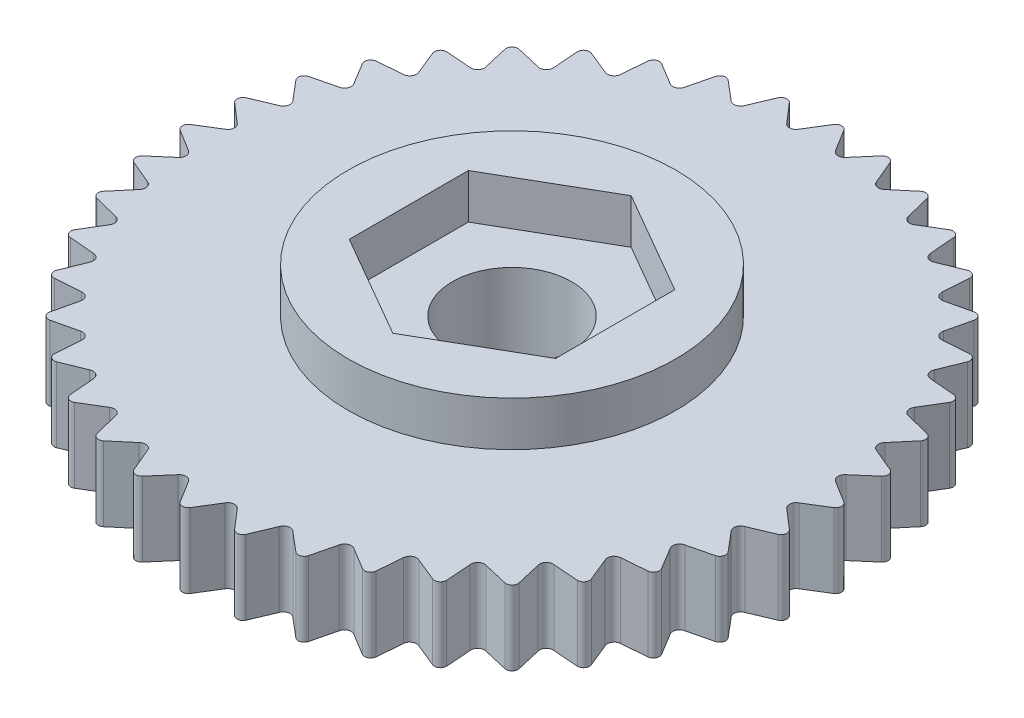
SolidWorks part; units mm, degrees
ref_plane "Front Plane" through (0, 0, 0) normal (0, 0, 1) x (1, 0, 0)
ref_plane "Top Plane" through (0, 0, 0) normal (0, 1, 0) x (1, 0, 0)
ref_plane "Right Plane" through (0, 0, 0) normal (1, 0, 0) x (0, 0, -1)
sketch "Sketch1" plane through (0, 0, 0) normal (0, 1, 0) x (1, 0, 0)
  line L0 (0, 11.25) -> (0, -11.25) construction
  line L1 (0, 11.25) -> (-1.7599, 11.1115) construction
  line L2 (-1.7599, 11.1115) -> (-3.4764, 10.6994) construction
  line L3 (-3.4764, 10.6994) -> (-5.1074, 10.0238) construction
  line L4 (-5.1074, 10.0238) -> (-6.6126, 9.1014) construction
  line L5 (-6.6126, 9.1014) -> (-7.955, 7.955) construction
  line L6 (-7.955, 7.955) -> (-9.1014, 6.6126) construction
  line L7 (-9.1014, 6.6126) -> (-10.0238, 5.1074) construction
  line L8 (-10.0238, 5.1074) -> (-10.6994, 3.4764) construction
  line L9 (-10.6994, 3.4764) -> (-11.1115, 1.7599) construction
  line L10 (-11.1115, 1.7599) -> (-11.25, 0) construction
  line L11 (-11.25, 0) -> (-11.1115, -1.7599) construction
  line L12 (-11.1115, -1.7599) -> (-10.6994, -3.4764) construction
  line L13 (-10.6994, -3.4764) -> (-10.0238, -5.1074) construction
  line L14 (-10.0238, -5.1074) -> (-9.1014, -6.6126) construction
  line L15 (-9.1014, -6.6126) -> (-7.955, -7.955) construction
  line L16 (-7.955, -7.955) -> (-6.6126, -9.1014) construction
  line L17 (-6.6126, -9.1014) -> (-5.1074, -10.0238) construction
  line L18 (-5.1074, -10.0238) -> (-3.4764, -10.6994) construction
  line L19 (-3.4764, -10.6994) -> (-1.7599, -11.1115) construction
  line L20 (-1.7599, -11.1115) -> (0, -11.25) construction
  line L21 (0, -11.25) -> (1.7599, -11.1115) construction
  line L22 (1.7599, -11.1115) -> (3.4764, -10.6994) construction
  line L23 (3.4764, -10.6994) -> (5.1074, -10.0238) construction
  line L24 (5.1074, -10.0238) -> (6.6126, -9.1014) construction
  line L25 (6.6126, -9.1014) -> (7.955, -7.955) construction
  line L26 (7.955, -7.955) -> (9.1014, -6.6126) construction
  line L27 (9.1014, -6.6126) -> (10.0238, -5.1074) construction
  line L28 (10.0238, -5.1074) -> (10.6994, -3.4764) construction
  line L29 (10.6994, -3.4764) -> (11.1115, -1.7599) construction
  line L30 (11.1115, -1.7599) -> (11.25, 0) construction
  line L31 (11.25, 0) -> (11.1115, 1.7599) construction
  line L32 (11.1115, 1.7599) -> (10.6994, 3.4764) construction
  line L33 (10.6994, 3.4764) -> (10.0238, 5.1074) construction
  line L34 (10.0238, 5.1074) -> (9.1014, 6.6126) construction
  line L35 (9.1014, 6.6126) -> (7.955, 7.955) construction
  line L36 (7.955, 7.955) -> (6.6126, 9.1014) construction
  line L37 (6.6126, 9.1014) -> (5.1074, 10.0238) construction
  line L38 (5.1074, 10.0238) -> (3.4764, 10.6994) construction
  line L39 (3.4764, 10.6994) -> (1.7599, 11.1115) construction
  line L40 (1.7599, 11.1115) -> (0, 11.25) construction
  line L41 (0, 11.25) -> (-0.7858, 9.984) construction
  line L42 (-0.8799, 11.1807) -> (-0.7858, 9.984) construction
  line L43 (0, 11.25) -> (0.7858, 9.984) construction
  line L44 (-0.7858, 9.984) -> (0.7858, 9.984) construction
  line L45 (-0.1688, 10.9781) -> (0.1688, 10.9781) construction
  line L46 (-0.806, 10.241) -> (-0.617, 10.2559) construction
  line L47 (-0.1688, 10.9781) -> (-0.6316, 10.2324)
  line L48 (0.8799, 11.1807) -> (0.7858, 9.984) construction
  line L49 (0.617, 10.2559) -> (0.806, 10.241) construction
  line L50 (0.1688, 10.9781) -> (0.617, 10.2559)
  line L51 (1.5507, 10.8694) -> (0.9769, 10.2052)
  line L52 (1.884, 10.8166) -> (2.2138, 10.0331)
  line L53 (3.2319, 10.493) -> (2.5613, 9.9267)
  line L54 (3.5529, 10.3887) -> (3.7561, 9.5633)
  line L55 (4.8336, 9.8582) -> (4.0826, 9.4039)
  line L56 (5.1343, 9.705) -> (5.2058, 8.858)
  line L57 (6.3162, 8.9807) -> (5.5035, 8.6494)
  line L58 (6.5893, 8.7823) -> (6.5274, 7.9345)
  line L59 (7.6434, 7.882) -> (6.7888, 7.682)
  line L60 (7.882, 7.6434) -> (7.6883, 6.8157)
  line L61 (8.7823, 6.5893) -> (7.9069, 6.5254)
  line L62 (8.9807, 6.3162) -> (8.6599, 5.5291)
  line L63 (9.705, 5.1343) -> (8.8304, 5.2082)
  line L64 (9.8582, 4.8336) -> (9.4182, 4.1063)
  line L65 (10.3887, 3.5529) -> (9.5364, 3.7627)
  line L66 (10.493, 3.2319) -> (9.9446, 2.5824)
  line L67 (10.8166, 1.884) -> (10.0076, 2.2245)
  line L68 (10.8694, 1.5507) -> (10.2262, 0.995)
  line L69 (10.9781, 0.1688) -> (10.2324, 0.6316)
  line L70 (10.9781, -0.1688) -> (10.2559, -0.617)
  line L71 (10.8694, -1.5507) -> (10.2052, -0.9769)
  line L72 (10.8166, -1.884) -> (10.0331, -2.2138)
  line L73 (10.493, -3.2319) -> (9.9267, -2.5613)
  line L74 (10.3887, -3.5529) -> (9.5633, -3.7561)
  line L75 (9.8582, -4.8336) -> (9.4039, -4.0826)
  line L76 (9.705, -5.1343) -> (8.858, -5.2058)
  line L77 (8.9807, -6.3162) -> (8.6494, -5.5035)
  line L78 (8.7823, -6.5893) -> (7.9345, -6.5274)
  line L79 (7.882, -7.6434) -> (7.682, -6.7888)
  line L80 (7.6434, -7.882) -> (6.8157, -7.6883)
  line L81 (6.5893, -8.7823) -> (6.5254, -7.9069)
  line L82 (6.3162, -8.9807) -> (5.5291, -8.6599)
  line L83 (5.1343, -9.705) -> (5.2082, -8.8304)
  line L84 (4.8336, -9.8582) -> (4.1063, -9.4182)
  line L85 (3.5529, -10.3887) -> (3.7627, -9.5364)
  line L86 (3.2319, -10.493) -> (2.5824, -9.9446)
  line L87 (1.884, -10.8166) -> (2.2245, -10.0076)
  line L88 (1.5507, -10.8694) -> (0.995, -10.2262)
  line L89 (0.1688, -10.9781) -> (0.6316, -10.2324)
  line L90 (-0.1688, -10.9781) -> (-0.617, -10.2559)
  line L91 (-1.5507, -10.8694) -> (-0.9769, -10.2052)
  line L92 (-1.884, -10.8166) -> (-2.2138, -10.0331)
  line L93 (-3.2319, -10.493) -> (-2.5613, -9.9267)
  line L94 (-3.5529, -10.3887) -> (-3.7561, -9.5633)
  line L95 (-4.8336, -9.8582) -> (-4.0826, -9.4039)
  line L96 (-5.1343, -9.705) -> (-5.2058, -8.858)
  line L97 (-6.3162, -8.9807) -> (-5.5035, -8.6494)
  line L98 (-6.5893, -8.7823) -> (-6.5274, -7.9345)
  line L99 (-7.6434, -7.882) -> (-6.7888, -7.682)
  line L100 (-7.882, -7.6434) -> (-7.6883, -6.8157)
  line L101 (-8.7823, -6.5893) -> (-7.9069, -6.5254)
  line L102 (-8.9807, -6.3162) -> (-8.6599, -5.5291)
  line L103 (-9.705, -5.1343) -> (-8.8304, -5.2082)
  line L104 (-9.8582, -4.8336) -> (-9.4182, -4.1063)
  line L105 (-10.3887, -3.5529) -> (-9.5364, -3.7627)
  line L106 (-10.493, -3.2319) -> (-9.9446, -2.5824)
  line L107 (-10.8166, -1.884) -> (-10.0076, -2.2245)
  line L108 (-10.8694, -1.5507) -> (-10.2262, -0.995)
  line L109 (-10.9781, -0.1688) -> (-10.2324, -0.6316)
  line L110 (-10.9781, 0.1688) -> (-10.2559, 0.617)
  line L111 (-10.8694, 1.5507) -> (-10.2052, 0.9769)
  line L112 (-10.8166, 1.884) -> (-10.0331, 2.2138)
  line L113 (-10.493, 3.2319) -> (-9.9267, 2.5613)
  line L114 (-10.3887, 3.5529) -> (-9.5633, 3.7561)
  line L115 (-9.8582, 4.8336) -> (-9.4039, 4.0826)
  line L116 (-9.705, 5.1343) -> (-8.858, 5.2058)
  line L117 (-8.9807, 6.3162) -> (-8.6494, 5.5035)
  line L118 (-8.7823, 6.5893) -> (-7.9345, 6.5274)
  line L119 (-7.882, 7.6434) -> (-7.682, 6.7888)
  line L120 (-7.6434, 7.882) -> (-6.8157, 7.6883)
  line L121 (-6.5893, 8.7823) -> (-6.5254, 7.9069)
  line L122 (-6.3162, 8.9807) -> (-5.5291, 8.6599)
  line L123 (-5.1343, 9.705) -> (-5.2082, 8.8304)
  line L124 (-4.8336, 9.8582) -> (-4.1063, 9.4182)
  line L125 (-3.5529, 10.3887) -> (-3.7627, 9.5364)
  line L126 (-3.2319, 10.493) -> (-2.5824, 9.9446)
  line L127 (-1.884, 10.8166) -> (-2.2245, 10.0076)
  line L128 (-1.5507, 10.8694) -> (-0.995, 10.2262)
  circle A0 centre (0, 0) radius 11.25 construction
  circle A1 centre (0, 0) radius 5.5
  arc A2 (-0.1688, 10.9781) -> (0.1688, 10.9781) centre (0, 10.87) cw
  arc A3 (-0.617, 10.2559) -> (-0.7979, 10.138) centre (-0.8156, 10.3629) cw
  arc A4 (0.617, 10.2559) -> (0.7979, 10.138) centre (0.8156, 10.3629) ccw
  arc A5 (0.995, 10.2262) -> (0.7979, 10.138) centre (0.8156, 10.3629) cw
  arc A6 (1.5507, 10.8694) -> (1.884, 10.8166) centre (1.7004, 10.7362) cw
  arc A7 (2.2138, 10.0331) -> (2.374, 9.8884) centre (2.4266, 10.1077) ccw
  arc A8 (2.5824, 9.9446) -> (2.374, 9.8884) centre (2.4266, 10.1077) cw
  arc A9 (3.2319, 10.493) -> (3.5529, 10.3887) centre (3.359, 10.338) cw
  arc A10 (3.7561, 9.5633) -> (3.8916, 9.3953) centre (3.978, 9.6036) ccw
  arc A11 (4.1063, 9.4182) -> (3.8916, 9.3953) centre (3.978, 9.6036) cw
  arc A12 (4.8336, 9.8582) -> (5.1343, 9.705) centre (4.9349, 9.6852) cw
  arc A13 (5.2058, 8.858) -> (5.3135, 8.6708) centre (5.4313, 8.8631) ccw
  arc A14 (5.5291, 8.6599) -> (5.3135, 8.6708) centre (5.4313, 8.8631) cw
  arc A15 (6.3162, 8.9807) -> (6.5893, 8.7823) centre (6.3892, 8.794) cw
  arc A16 (6.5274, 7.9345) -> (6.6045, 7.7328) centre (6.7509, 7.9043) ccw
  arc A17 (6.8157, 7.6883) -> (6.6045, 7.7328) centre (6.7509, 7.9043) cw
  arc A18 (7.6434, 7.882) -> (7.882, 7.6434) centre (7.6863, 7.6863) cw
  arc A19 (7.6883, 6.8157) -> (7.7328, 6.6045) centre (7.9043, 6.7509) ccw
  arc A20 (7.9345, 6.5274) -> (7.7328, 6.6045) centre (7.9043, 6.7509) cw
  arc A21 (8.7823, 6.5893) -> (8.9807, 6.3162) centre (8.794, 6.3892) cw
  arc A22 (8.6599, 5.5291) -> (8.6708, 5.3135) centre (8.8631, 5.4313) ccw
  arc A23 (8.858, 5.2058) -> (8.6708, 5.3135) centre (8.8631, 5.4313) cw
  arc A24 (9.705, 5.1343) -> (9.8582, 4.8336) centre (9.6852, 4.9349) cw
  arc A25 (9.4182, 4.1063) -> (9.3953, 3.8916) centre (9.6036, 3.978) ccw
  arc A26 (9.5633, 3.7561) -> (9.3953, 3.8916) centre (9.6036, 3.978) cw
  arc A27 (10.3887, 3.5529) -> (10.493, 3.2319) centre (10.338, 3.359) cw
  arc A28 (9.9446, 2.5824) -> (9.8884, 2.374) centre (10.1077, 2.4266) ccw
  arc A29 (10.0331, 2.2138) -> (9.8884, 2.374) centre (10.1077, 2.4266) cw
  arc A30 (10.8166, 1.884) -> (10.8694, 1.5507) centre (10.7362, 1.7004) cw
  arc A31 (10.2262, 0.995) -> (10.138, 0.7979) centre (10.3629, 0.8156) ccw
  arc A32 (10.2559, 0.617) -> (10.138, 0.7979) centre (10.3629, 0.8156) cw
  arc A33 (10.9781, 0.1688) -> (10.9781, -0.1688) centre (10.87, 0) cw
  arc A34 (10.2559, -0.617) -> (10.138, -0.7979) centre (10.3629, -0.8156) ccw
  arc A35 (10.2262, -0.995) -> (10.138, -0.7979) centre (10.3629, -0.8156) cw
  arc A36 (10.8694, -1.5507) -> (10.8166, -1.884) centre (10.7362, -1.7004) cw
  arc A37 (10.0331, -2.2138) -> (9.8884, -2.374) centre (10.1077, -2.4266) ccw
  arc A38 (9.9446, -2.5824) -> (9.8884, -2.374) centre (10.1077, -2.4266) cw
  arc A39 (10.493, -3.2319) -> (10.3887, -3.5529) centre (10.338, -3.359) cw
  arc A40 (9.5633, -3.7561) -> (9.3953, -3.8916) centre (9.6036, -3.978) ccw
  arc A41 (9.4182, -4.1063) -> (9.3953, -3.8916) centre (9.6036, -3.978) cw
  arc A42 (9.8582, -4.8336) -> (9.705, -5.1343) centre (9.6852, -4.9349) cw
  arc A43 (8.858, -5.2058) -> (8.6708, -5.3135) centre (8.8631, -5.4313) ccw
  arc A44 (8.6599, -5.5291) -> (8.6708, -5.3135) centre (8.8631, -5.4313) cw
  arc A45 (8.9807, -6.3162) -> (8.7823, -6.5893) centre (8.794, -6.3892) cw
  arc A46 (7.9345, -6.5274) -> (7.7328, -6.6045) centre (7.9043, -6.7509) ccw
  arc A47 (7.6883, -6.8157) -> (7.7328, -6.6045) centre (7.9043, -6.7509) cw
  arc A48 (7.882, -7.6434) -> (7.6434, -7.882) centre (7.6863, -7.6863) cw
  arc A49 (6.8157, -7.6883) -> (6.6045, -7.7328) centre (6.7509, -7.9043) ccw
  arc A50 (6.5274, -7.9345) -> (6.6045, -7.7328) centre (6.7509, -7.9043) cw
  arc A51 (6.5893, -8.7823) -> (6.3162, -8.9807) centre (6.3892, -8.794) cw
  arc A52 (5.5291, -8.6599) -> (5.3135, -8.6708) centre (5.4313, -8.8631) ccw
  arc A53 (5.2058, -8.858) -> (5.3135, -8.6708) centre (5.4313, -8.8631) cw
  arc A54 (5.1343, -9.705) -> (4.8336, -9.8582) centre (4.9349, -9.6852) cw
  arc A55 (4.1063, -9.4182) -> (3.8916, -9.3953) centre (3.978, -9.6036) ccw
  arc A56 (3.7561, -9.5633) -> (3.8916, -9.3953) centre (3.978, -9.6036) cw
  arc A57 (3.5529, -10.3887) -> (3.2319, -10.493) centre (3.359, -10.338) cw
  arc A58 (2.5824, -9.9446) -> (2.374, -9.8884) centre (2.4266, -10.1077) ccw
  arc A59 (2.2138, -10.0331) -> (2.374, -9.8884) centre (2.4266, -10.1077) cw
  arc A60 (1.884, -10.8166) -> (1.5507, -10.8694) centre (1.7004, -10.7362) cw
  arc A61 (0.995, -10.2262) -> (0.7979, -10.138) centre (0.8156, -10.3629) ccw
  arc A62 (0.617, -10.2559) -> (0.7979, -10.138) centre (0.8156, -10.3629) cw
  arc A63 (0.1688, -10.9781) -> (-0.1688, -10.9781) centre (0, -10.87) cw
  arc A64 (-0.617, -10.2559) -> (-0.7979, -10.138) centre (-0.8156, -10.3629) ccw
  arc A65 (-0.995, -10.2262) -> (-0.7979, -10.138) centre (-0.8156, -10.3629) cw
  arc A66 (-1.5507, -10.8694) -> (-1.884, -10.8166) centre (-1.7004, -10.7362) cw
  arc A67 (-2.2138, -10.0331) -> (-2.374, -9.8884) centre (-2.4266, -10.1077) ccw
  arc A68 (-2.5824, -9.9446) -> (-2.374, -9.8884) centre (-2.4266, -10.1077) cw
  arc A69 (-3.2319, -10.493) -> (-3.5529, -10.3887) centre (-3.359, -10.338) cw
  arc A70 (-3.7561, -9.5633) -> (-3.8916, -9.3953) centre (-3.978, -9.6036) ccw
  arc A71 (-4.1063, -9.4182) -> (-3.8916, -9.3953) centre (-3.978, -9.6036) cw
  arc A72 (-4.8336, -9.8582) -> (-5.1343, -9.705) centre (-4.9349, -9.6852) cw
  arc A73 (-5.2058, -8.858) -> (-5.3135, -8.6708) centre (-5.4313, -8.8631) ccw
  arc A74 (-5.5291, -8.6599) -> (-5.3135, -8.6708) centre (-5.4313, -8.8631) cw
  arc A75 (-6.3162, -8.9807) -> (-6.5893, -8.7823) centre (-6.3892, -8.794) cw
  arc A76 (-6.5274, -7.9345) -> (-6.6045, -7.7328) centre (-6.7509, -7.9043) ccw
  arc A77 (-6.8157, -7.6883) -> (-6.6045, -7.7328) centre (-6.7509, -7.9043) cw
  arc A78 (-7.6434, -7.882) -> (-7.882, -7.6434) centre (-7.6863, -7.6863) cw
  arc A79 (-7.6883, -6.8157) -> (-7.7328, -6.6045) centre (-7.9043, -6.7509) ccw
  arc A80 (-7.9345, -6.5274) -> (-7.7328, -6.6045) centre (-7.9043, -6.7509) cw
  arc A81 (-8.7823, -6.5893) -> (-8.9807, -6.3162) centre (-8.794, -6.3892) cw
  arc A82 (-8.6599, -5.5291) -> (-8.6708, -5.3135) centre (-8.8631, -5.4313) ccw
  arc A83 (-8.858, -5.2058) -> (-8.6708, -5.3135) centre (-8.8631, -5.4313) cw
  arc A84 (-9.705, -5.1343) -> (-9.8582, -4.8336) centre (-9.6852, -4.9349) cw
  arc A85 (-9.4182, -4.1063) -> (-9.3953, -3.8916) centre (-9.6036, -3.978) ccw
  arc A86 (-9.5633, -3.7561) -> (-9.3953, -3.8916) centre (-9.6036, -3.978) cw
  arc A87 (-10.3887, -3.5529) -> (-10.493, -3.2319) centre (-10.338, -3.359) cw
  arc A88 (-9.9446, -2.5824) -> (-9.8884, -2.374) centre (-10.1077, -2.4266) ccw
  arc A89 (-10.0331, -2.2138) -> (-9.8884, -2.374) centre (-10.1077, -2.4266) cw
  arc A90 (-10.8166, -1.884) -> (-10.8694, -1.5507) centre (-10.7362, -1.7004) cw
  arc A91 (-10.2262, -0.995) -> (-10.138, -0.7979) centre (-10.3629, -0.8156) ccw
  arc A92 (-10.2559, -0.617) -> (-10.138, -0.7979) centre (-10.3629, -0.8156) cw
  arc A93 (-10.9781, -0.1688) -> (-10.9781, 0.1688) centre (-10.87, 0) cw
  arc A94 (-10.2559, 0.617) -> (-10.138, 0.7979) centre (-10.3629, 0.8156) ccw
  arc A95 (-10.2262, 0.995) -> (-10.138, 0.7979) centre (-10.3629, 0.8156) cw
  arc A96 (-10.8694, 1.5507) -> (-10.8166, 1.884) centre (-10.7362, 1.7004) cw
  arc A97 (-10.0331, 2.2138) -> (-9.8884, 2.374) centre (-10.1077, 2.4266) ccw
  arc A98 (-9.9446, 2.5824) -> (-9.8884, 2.374) centre (-10.1077, 2.4266) cw
  arc A99 (-10.493, 3.2319) -> (-10.3887, 3.5529) centre (-10.338, 3.359) cw
  arc A100 (-9.5633, 3.7561) -> (-9.3953, 3.8916) centre (-9.6036, 3.978) ccw
  arc A101 (-9.4182, 4.1063) -> (-9.3953, 3.8916) centre (-9.6036, 3.978) cw
  arc A102 (-9.8582, 4.8336) -> (-9.705, 5.1343) centre (-9.6852, 4.9349) cw
  arc A103 (-8.858, 5.2058) -> (-8.6708, 5.3135) centre (-8.8631, 5.4313) ccw
  arc A104 (-8.6599, 5.5291) -> (-8.6708, 5.3135) centre (-8.8631, 5.4313) cw
  arc A105 (-8.9807, 6.3162) -> (-8.7823, 6.5893) centre (-8.794, 6.3892) cw
  arc A106 (-7.9345, 6.5274) -> (-7.7328, 6.6045) centre (-7.9043, 6.7509) ccw
  arc A107 (-7.6883, 6.8157) -> (-7.7328, 6.6045) centre (-7.9043, 6.7509) cw
  arc A108 (-7.882, 7.6434) -> (-7.6434, 7.882) centre (-7.6863, 7.6863) cw
  arc A109 (-6.8157, 7.6883) -> (-6.6045, 7.7328) centre (-6.7509, 7.9043) ccw
  arc A110 (-6.5274, 7.9345) -> (-6.6045, 7.7328) centre (-6.7509, 7.9043) cw
  arc A111 (-6.5893, 8.7823) -> (-6.3162, 8.9807) centre (-6.3892, 8.794) cw
  arc A112 (-5.5291, 8.6599) -> (-5.3135, 8.6708) centre (-5.4313, 8.8631) ccw
  arc A113 (-5.2058, 8.858) -> (-5.3135, 8.6708) centre (-5.4313, 8.8631) cw
  arc A114 (-5.1343, 9.705) -> (-4.8336, 9.8582) centre (-4.9349, 9.6852) cw
  arc A115 (-4.1063, 9.4182) -> (-3.8916, 9.3953) centre (-3.978, 9.6036) ccw
  arc A116 (-3.7561, 9.5633) -> (-3.8916, 9.3953) centre (-3.978, 9.6036) cw
  arc A117 (-3.5529, 10.3887) -> (-3.2319, 10.493) centre (-3.359, 10.338) cw
  arc A118 (-2.5824, 9.9446) -> (-2.374, 9.8884) centre (-2.4266, 10.1077) ccw
  arc A119 (-2.2138, 10.0331) -> (-2.374, 9.8884) centre (-2.4266, 10.1077) cw
  arc A120 (-1.884, 10.8166) -> (-1.5507, 10.8694) centre (-1.7004, 10.7362) cw
  arc A121 (-0.995, 10.2262) -> (-0.7979, 10.138) centre (-0.8156, 10.3629) ccw
  point P453 (0, 0)
  dimension "D2" = 11
  dimension "D1" = 22.5
  dimension "D3" = 1.49
  dimension "D4" = 0.38
  dimension "D5" = 0.32
  dimension "D6" = 0.38
  dimension "D7" = 0.32
  dimension "D8" = 0.38
  dimension "D9" = 0.32
  dimension "D10" = 40
extrude "Boss-Extrude1" add sketch "Sketch1" along normal blind 2.5 contours A121 L128 A120 L127 A119 A118 L126 A117 L125 A116 A115 L124 A114 L123 A113 A112 L122 A111 L121 A110 A109 L120 A108 L119 A107 A106 L118 A105 L117 A104 A103 L116 A102 L115 A101 A100 L114 A99 L113 A98 A97 L112 A96
sketch "Sketch2" plane through (0, 0, 0) normal (0, 1, 0) x (1, 0, 0)
  line L0 (0, 4.0025) -> (0, -4.0025) construction
  line L1 (0, 4.0025) -> (-3.4663, 2.0013)
  line L2 (-3.4663, 2.0013) -> (-3.4663, -2.0013)
  line L3 (-3.4663, -2.0013) -> (0, -4.0025)
  line L4 (0, -4.0025) -> (3.4663, -2.0013)
  line L5 (3.4663, -2.0013) -> (3.4663, 2.0013)
  line L6 (3.4663, 2.0013) -> (0, 4.0025)
  circle A0 centre (0, 0) radius 5.5 construction
  circle A1 centre (0, 0) radius 5.5
  circle A2 centre (0, 0) radius 4.0025 construction
  dimension "D1" = 8.005
extrude "Boss-Extrude2" add sketch "Sketch2" along normal blind 4
sketch "Sketch3" plane through (0, 0, 0) normal (0, 1, 0) x (1, 0, 0)
  line L0 (3.4663, 2.0013) -> (0, 4.0025) construction
  line L1 (0, 4.0025) -> (-3.4663, 2.0013) construction
  line L2 (3.4663, -2.0013) -> (3.4663, 2.0013) construction
  line L3 (0, -4.0025) -> (3.4663, -2.0013) construction
  line L4 (-3.4663, -2.0013) -> (0, -4.0025) construction
  line L5 (-3.4663, 2.0013) -> (-3.4663, -2.0013) construction
  line L6 (0, 4.0025) -> (-3.4663, 2.0013)
  line L7 (3.4663, 2.0013) -> (0, 4.0025)
  line L8 (3.4663, -2.0013) -> (3.4663, 2.0013)
  line L9 (0, -4.0025) -> (3.4663, -2.0013)
  line L10 (-3.4663, -2.0013) -> (0, -4.0025)
  line L11 (-3.4663, 2.0013) -> (-3.4663, -2.0013)
  circle A0 centre (0, 0) radius 2.0025
  dimension "D1" = 4.005
extrude "Boss-Extrude3" add sketch "Sketch3" along normal blind 2.5
sketch "Axis" plane through (0, 0, 0) normal (1, 0, 0) x (0, 0, -1)
  line L0 (0, 0) -> (0, 4) construction
  line L1 (5.5, 4) -> (-5.5, 4) construction
